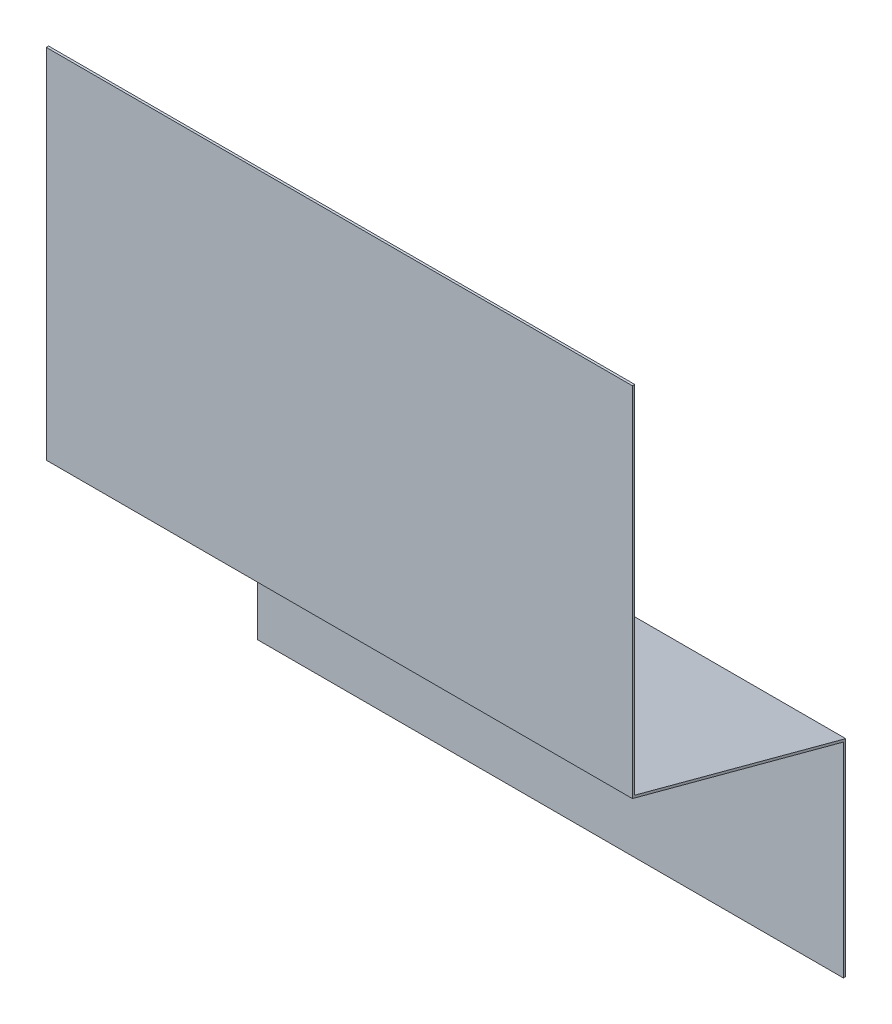
SolidWorks part; units mm, degrees
material "6061-T6 (SS)"
ref_plane "Front Plane" through (0, 0, 0) normal (0, 0, 1) x (1, 0, 0)
ref_plane "Top Plane" through (0, 0, 0) normal (0, 1, 0) x (1, 0, 0)
ref_plane "Right Plane" through (0, 0, 0) normal (1, 0, 0) x (0, 0, -1)
sketch "Sketch1" plane through (0, 0, 0) normal (1, 0, 0) x (0, 0, -1)
  line L0 (0, 0) -> (0, 139.7)
  line L1 (0, 139.7) -> (-143.002, 178.0173)
  line L2 (-143.002, 178.0173) -> (-143.002, 419.1)
  line L3 (0, 139.7) -> (-143.1131, 139.7) construction
  dimension "D1" = 139.7
  dimension "D2" = 15
  dimension "D3" = 143.002
  dimension "D4" = 419.1
extrude "Extrude-Thin1" add sketch "Sketch1" along normal blind 397.256 thin thin type one direction reverse wall 1.5875
